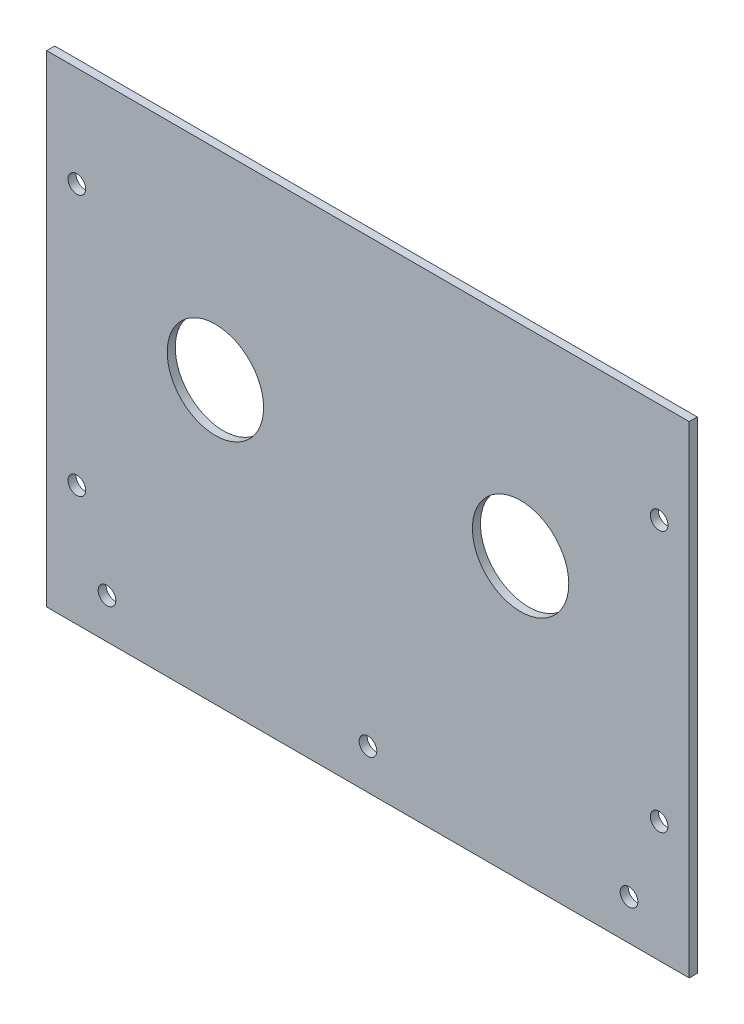
SolidWorks part; units mm, degrees
ref_plane "正面" through (0, 0, 0) normal (0, 0, 1) x (1, 0, 0)
ref_plane "平面" through (0, 0, 0) normal (0, 1, 0) x (1, 0, 0)
ref_plane "右側面" through (0, 0, 0) normal (1, 0, 0) x (0, 0, -1)
sketch "ｽｹｯﾁ1" plane through (0, 0, 0) normal (0, 0, 1) x (1, 0, 0)
  line L1 (-80, 60) -> (80, 60)
  line L2 (-80, 60) -> (-80, -60)
  line L3 (-80, -60) -> (80, -60)
  line L4 (80, 60) -> (80, -60)
  line L5 (-80, 60) -> (80, -60) construction
  line L6 (-80, -60) -> (80, 60) construction
  point P0 (0, 0)
  dimension "D1" = 160
  dimension "D2" = 120
extrude "ﾎﾞｽ - 押し出し1" add sketch "ｽｹｯﾁ1" along normal blind 2
sketch "ｽｹｯﾁ2" plane through (0, 0, 2) normal (0, 0, 1) x (1, 0, 0)
  line L0 (0, -60) -> (0, -40)
  line L1 (-80, -60) -> (80, -60) construction
  line L2 (0, -40) -> (0, 10)
  line L4 (0, 10) -> (-38, 10)
  line L5 (0, 10) -> (38, 10)
  line L6 (0, -60) -> (0, -50)
  line L7 (0, -50) -> (-65, -50)
  line L8 (0, -50) -> (65, -50)
  circle A0 centre (38, 10) radius 12
  circle A1 centre (-38, 10) radius 12
  circle A2 centre (-65, -50) radius 2.2
  circle A3 centre (65, -50) radius 2.2
  circle A4 centre (0, -50) radius 2.2
  dimension "D5" = 24
  dimension "D6" = 24
  dimension "D10" = 4.4
  dimension "D11" = 4.4
  dimension "D12" = 4.4
  dimension "D1" = 20
  dimension "D2" = 50
  dimension "D3" = 38
  dimension "D4" = 38
  dimension "D7" = 10
  dimension "D8" = 65
  dimension "D9" = 65
extrude "ｶｯﾄ - 押し出し1" cut sketch "ｽｹｯﾁ2" against normal blind 2
sketch "ｽｹｯﾁ4" plane through (0, 0, 2) normal (0, 0, 1) x (1, 0, 0)
  line L0 (80, 60) -> (72.5, 60)
  line L1 (80, 60) -> (-80, 60) construction
  line L2 (72.5, 60) -> (72.5, 35)
  line L3 (72.5, 35) -> (72.5, -30)
  line L4 (-80, 60) -> (-72.5, 60)
  line L5 (-72.5, 60) -> (-72.5, 35)
  line L6 (-72.5, 35) -> (-72.5, -30)
  circle A0 centre (72.5, 35) radius 2.2
  circle A1 centre (72.5, -30) radius 2.2
  circle A2 centre (-72.5, 35) radius 2.2
  circle A3 centre (-72.5, -30) radius 2.2
  dimension "D3" = 4.4
  dimension "D5" = 4.4
  dimension "D9" = 4.4
  dimension "D10" = 4.4
  dimension "D1" = 7.5
  dimension "D2" = 25
  dimension "D4" = 65
  dimension "D6" = 7.5
  dimension "D7" = 25
  dimension "D8" = 65
extrude "ｶｯﾄ - 押し出し2" cut sketch "ｽｹｯﾁ4" against normal blind 105
